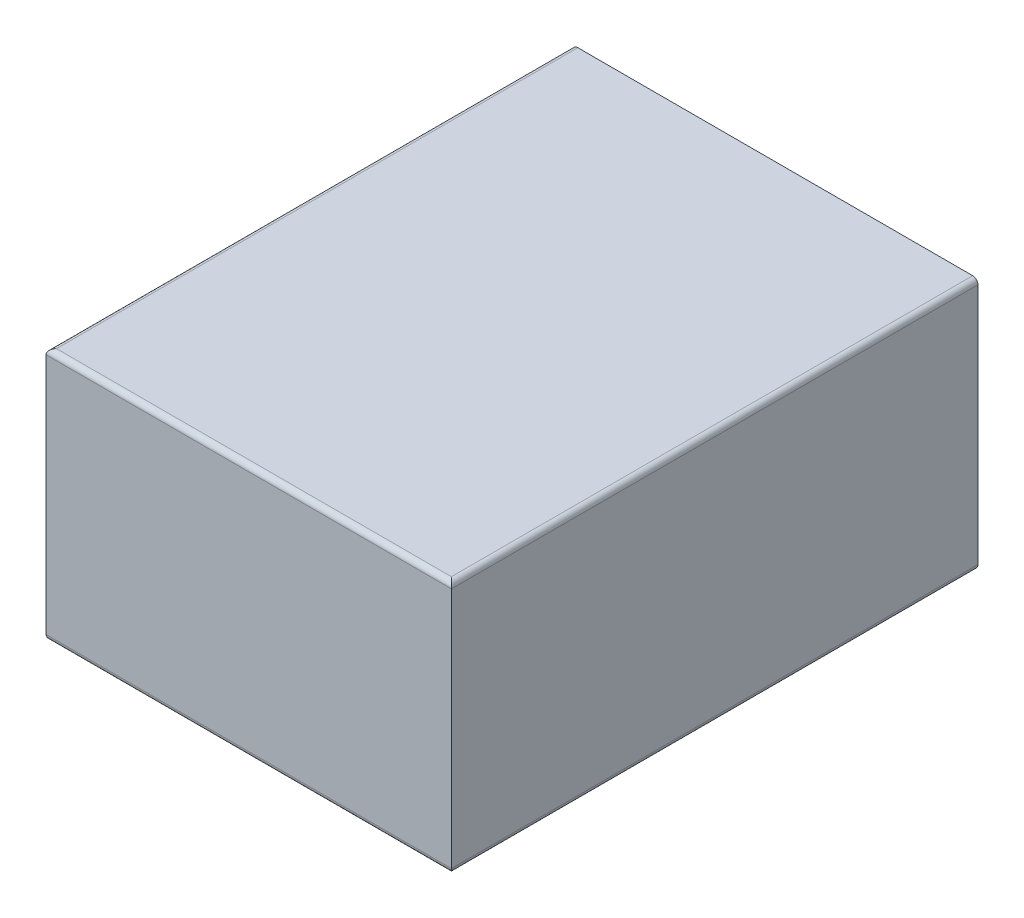
SolidWorks part; units mm, degrees
ref_plane "Alzado" through (0, 0, 0) normal (0, 0, 1) x (1, 0, 0)
ref_plane "Planta" through (0, 0, 0) normal (0, 1, 0) x (1, 0, 0)
ref_plane "Vista lateral" through (0, 0, 0) normal (1, 0, 0) x (0, 0, -1)
sketch "Croquis1" plane through (0, 0, 0) normal (0, 0, 1) x (1, 0, 0)
  line L1 (-385, -240) -> (385, -240)
  line L2 (-385, -240) -> (-385, 240)
  line L3 (-385, 240) -> (385, 240)
  line L4 (385, -240) -> (385, 240)
  line L5 (-385, -240) -> (385, 240) construction
  line L6 (-385, 240) -> (385, -240) construction
  point P0 (0, 0)
  dimension "D1" = 770
  dimension "D2" = 480
extrude "Saliente-Extruir1" add sketch "Croquis1" along normal blind 1000
fillet "Redondeo1" radius 10 6 edges at (0, 240, 1000) (0, -240, 1000) (-385, -240, 500) (385, -240, 500) (-385, 240, 500) (385, 240, 500)
